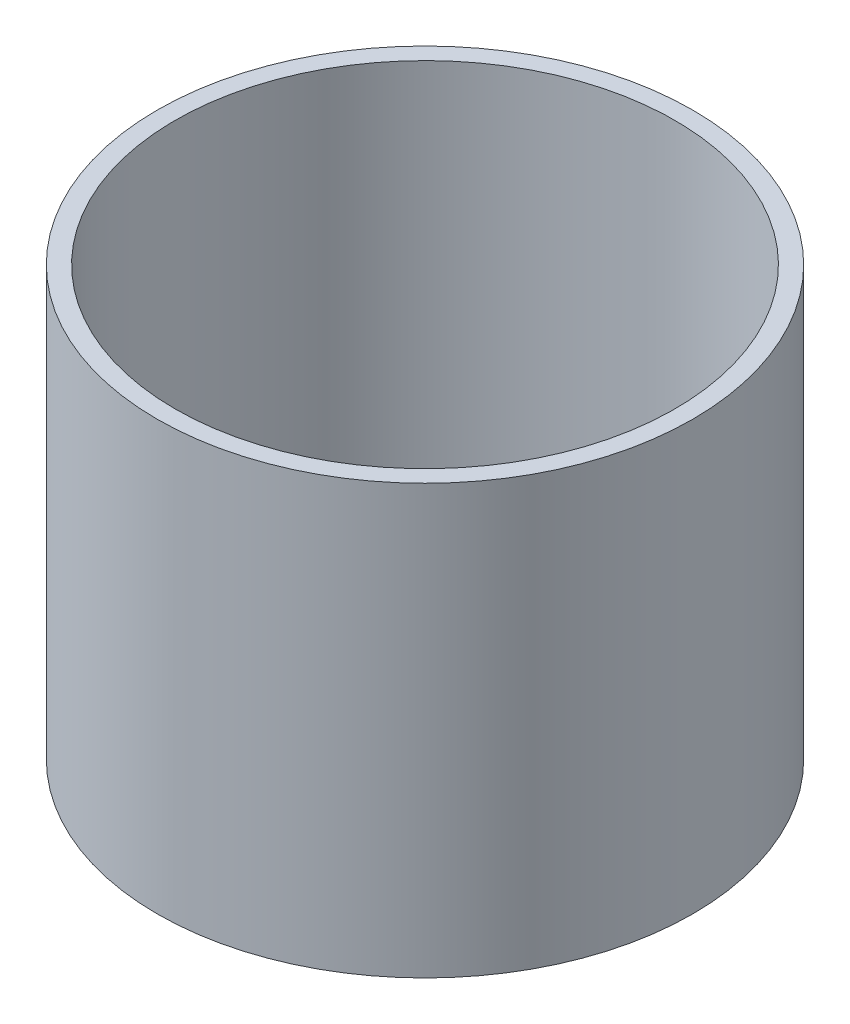
SolidWorks part; units mm, degrees
material "7075-T6 (SN)"
ref_plane "Front Plane" through (0, 0, 0) normal (0, 0, 1) x (1, 0, 0)
ref_plane "Top Plane" through (0, 0, 0) normal (0, 1, 0) x (1, 0, 0)
ref_plane "Right Plane" through (0, 0, 0) normal (1, 0, 0) x (0, 0, -1)
sketch "Sketch1" plane through (0, 0, 0) normal (0, 1, 0) x (1, 0, 0)
  circle A0 centre (0, 0) radius 47.625
  circle A1 centre (0, 0) radius 44.45
  dimension "D1" = 95.25
  dimension "D2" = 88.9
extrude "Boss-Extrude1" add sketch "Sketch1" along normal blind 76.2
